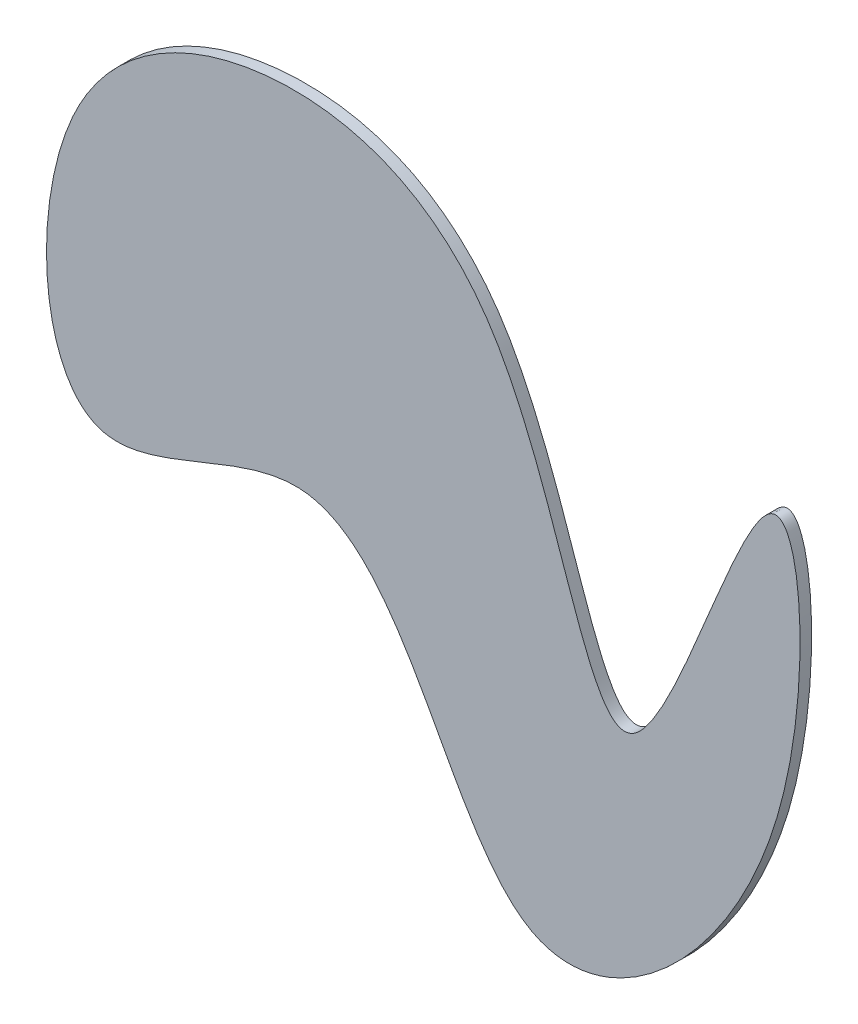
SolidWorks part; units mm, degrees
ref_plane "Front Plane" through (0, 0, 0) normal (0, 0, 1) x (1, 0, 0)
ref_plane "Top Plane" through (0, 0, 0) normal (0, 1, 0) x (1, 0, 0)
ref_plane "Right Plane" through (0, 0, 0) normal (1, 0, 0) x (0, 0, -1)
sketch "Sketch1" plane through (0, 0, 0) normal (0, 0, 1) x (1, 0, 0)
  spline S0 degree 3 poles (-23.5171, 72.2283) (-78.2801, 45.4274) (-74.0209, -42.1229) (1.0515, 16.028) (22.3994, -103.4943) (97.1471, -34.8428) (89.585, 76.5505) (49.8832, -66.9486) (34.9677, 51.3565) (-23.5171, 72.2283) (-78.2801, 45.4274) (-74.0209, -42.1229) knots -0.318991 -0.191455 -0.097556 0 0.103469 0.185363 0.327108 0.460003 0.563109 0.681009 0.808545 0.902444 1 1.103469 1.185363 1.327108 only from (-67.6786, 35.6164) to (-67.6786, 35.6164)
extrude "Boss-Extrude1" add sketch "Sketch1" along normal blind 2.54
